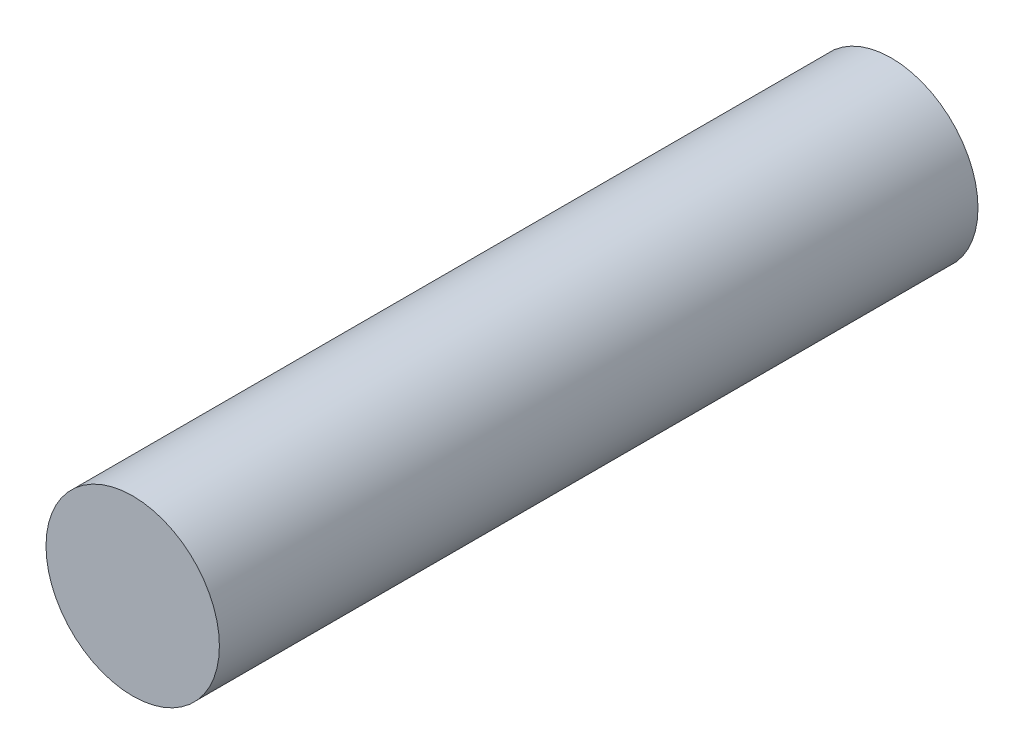
SolidWorks part; units mm, degrees
ref_plane "Front Plane" through (0, 0, 0) normal (0, 0, 1) x (1, 0, 0)
ref_plane "Top Plane" through (0, 0, 0) normal (0, 1, 0) x (1, 0, 0)
ref_plane "Right Plane" through (0, 0, 0) normal (1, 0, 0) x (0, 0, -1)
sketch "Sketch1" plane through (0, 0, 0) normal (0, 1, 0) x (1, 0, 0)
  line L1 (0, 0) -> (4, 0)
  line L2 (0, 0) -> (0, 35)
  line L3 (0, 35) -> (4, 35)
  line L4 (4, 0) -> (4, 35)
  dimension "D1" = 4
  dimension "D2" = 35
revolve "Revolve1" add sketch "Sketch1" angle 360 about L2
scale "Scale1" scale about centroid uniform scaling yes scale factor 0.5
